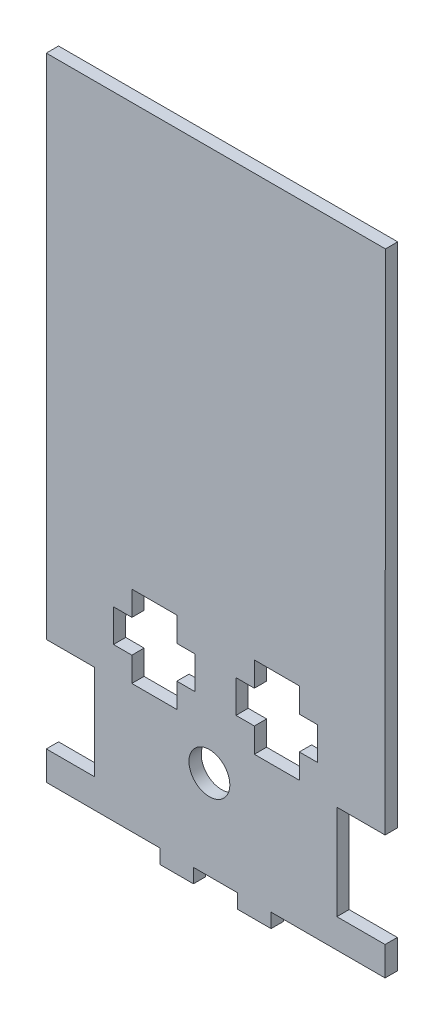
SolidWorks part; units mm, degrees
ref_plane "Alzado" through (0, 0, 0) normal (0, 0, 1) x (1, 0, 0)
ref_plane "Planta" through (0, 0, 0) normal (0, 1, 0) x (1, 0, 0)
ref_plane "Vista lateral" through (0, 0, 0) normal (1, 0, 0) x (0, 0, -1)
sketch "Model" plane through (0, 0, 0) normal (0, 0, 1) x (1, 0, 0)
  line L0 (25.0453, -23.1063) -> (25.0525, -17.1063)
  line L1 (36.0453, -23.1195) -> (25.0453, -23.1063)
  line L2 (36.0525, -17.1195) -> (36.0453, -23.1195)
  line L3 (20.5525, -17.1009) -> (25.0525, -17.1063)
  line L4 (20.5621, -9.1009) -> (20.5525, -17.1009)
  line L5 (25.0621, -9.1063) -> (20.5621, -9.1009)
  line L6 (25.0693, -3.1063) -> (25.0621, -9.1063)
  line L7 (36.0693, -3.1195) -> (25.0693, -3.1063)
  line L8 (36.0621, -9.1195) -> (36.0693, -3.1195)
  line L9 (40.5621, -9.1249) -> (36.0621, -9.1195)
  line L10 (40.5525, -17.1249) -> (40.5621, -9.1249)
  line L11 (36.0525, -17.1195) -> (40.5525, -17.1249)
  line L12 (66.0302, -23.1309) -> (66.0302, -17.1309)
  line L13 (55.0302, -23.1309) -> (66.0302, -23.1309)
  line L14 (55.0302, -17.1309) -> (55.0302, -23.1309)
  line L15 (70.5302, -17.1309) -> (66.0302, -17.1309)
  line L16 (70.5302, -9.1309) -> (70.5302, -17.1309)
  line L17 (66.0302, -9.1309) -> (70.5302, -9.1309)
  line L18 (66.0302, -3.1309) -> (66.0302, -9.1309)
  line L19 (55.0302, -3.1309) -> (66.0302, -3.1309)
  line L20 (55.0302, -9.1309) -> (55.0302, -3.1309)
  line L21 (50.5302, -9.1309) -> (55.0302, -9.1309)
  line L22 (50.5302, -17.1309) -> (50.5302, -9.1309)
  line L23 (55.0302, -17.1309) -> (50.5302, -17.1309)
  line L24 (4.1116, 100.0157) -> (4.1116, -10.669)
  line L25 (4.1116, -10.669) -> (4.1116, -24.2466)
  line L26 (4.1116, -24.2466) -> (15.9116, -24.2466)
  line L27 (15.9116, -24.2466) -> (15.9116, -47.4466)
  line L28 (15.9116, -47.4466) -> (4.1116, -47.4466)
  line L29 (4.1116, -47.4466) -> (4.1116, -54.5314)
  line L30 (4.1116, -54.5314) -> (31.9189, -54.5455)
  line L31 (31.9189, -54.5455) -> (31.9189, -58.039)
  line L32 (31.9189, -58.039) -> (40.1189, -58.039)
  line L33 (40.1189, -58.039) -> (40.1189, -54.539)
  line L34 (40.1189, -54.539) -> (50.9189, -54.539)
  line L35 (50.9189, -54.539) -> (50.9189, -58.039)
  line L36 (50.9189, -58.039) -> (59.1189, -58.039)
  line L37 (59.1189, -58.039) -> (59.1189, -54.539)
  line L38 (59.1189, -54.539) -> (87.0189, -54.5466)
  line L39 (87.0189, -54.5466) -> (87.0189, -47.4466)
  line L40 (87.0189, -47.4466) -> (75.2189, -47.4466)
  line L41 (75.2189, -47.4466) -> (75.2189, -24.2466)
  line L42 (75.2189, -24.2466) -> (87.0189, -24.2466)
  line L43 (87.0189, -24.2466) -> (87.1116, 100.0157)
  line L44 (87.1116, 100.0157) -> (4.1116, 100.0157)
  circle A0 centre (44.0265, -32.6326) radius 5
extrude "Saliente-Extruir1" add sketch "Model" along normal blind 3
